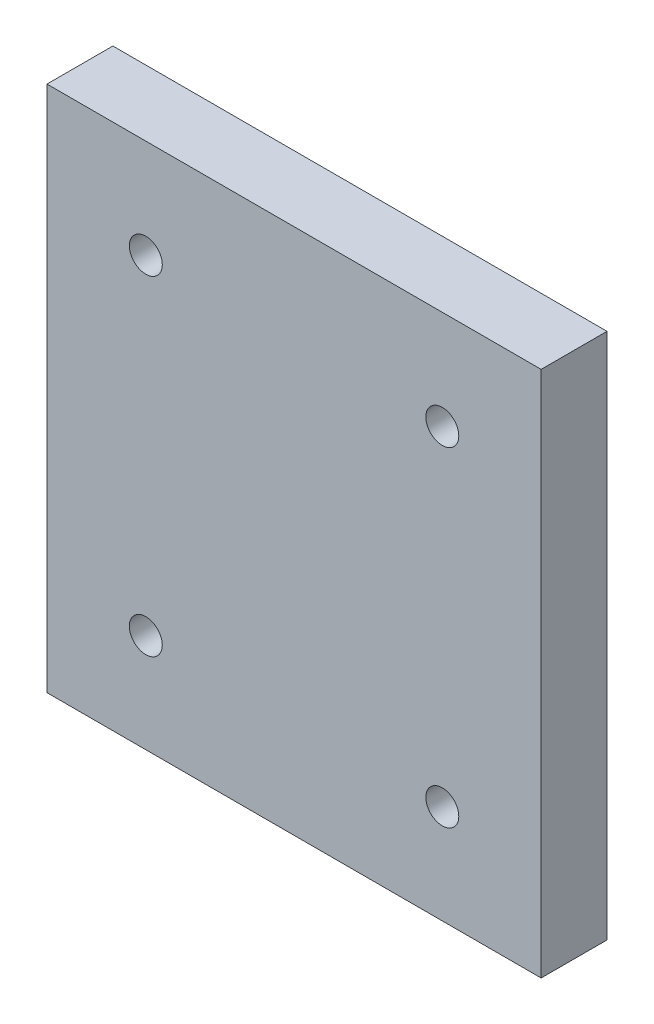
SolidWorks part; units mm, degrees
ref_plane "Front Plane" through (0, 0, 0) normal (0, 0, 1) x (1, 0, 0)
ref_plane "Top Plane" through (0, 0, 0) normal (0, 1, 0) x (1, 0, 0)
ref_plane "Right Plane" through (0, 0, 0) normal (1, 0, 0) x (0, 0, -1)
sketch "Sketch1" plane through (0, 0, 0) normal (0, 0, 1) x (1, 0, 0)
  line L0 (2.5, 60) -> (52.5, 60) construction
  line L1 (55, 60) -> (0, 60)
  line L2 (55, 60) -> (55, 0)
  line L3 (55, 0) -> (0, 0)
  line L4 (0, 60) -> (0, 0)
  line L5 (55, 2.5) -> (55, 57.5) construction
  line L6 (2.5, 0) -> (52.5, 0) construction
  line L7 (0, 2.5) -> (0, 57.5) construction
  line L8 (65, 70) -> (65, -10)
  line L9 (65, -10) -> (-10, -10)
  line L10 (-10, 70) -> (-10, -10)
  line L11 (65, 70) -> (-10, 70)
  circle A0 centre (50, 55) radius 2.5
  circle A1 centre (5, 55) radius 2.5
  circle A2 centre (5, 5) radius 2.5
  circle A3 centre (50, 5) radius 2.5
  dimension "D1" = 5
  dimension "D2" = 10
extrude "Boss-Extrude1" add sketch "Sketch1" along normal blind 10 contours L1 L4 L3 L2 A3 A2 A1 A0 | L8 L11 L10 L9 L4 L1 L2 L3
